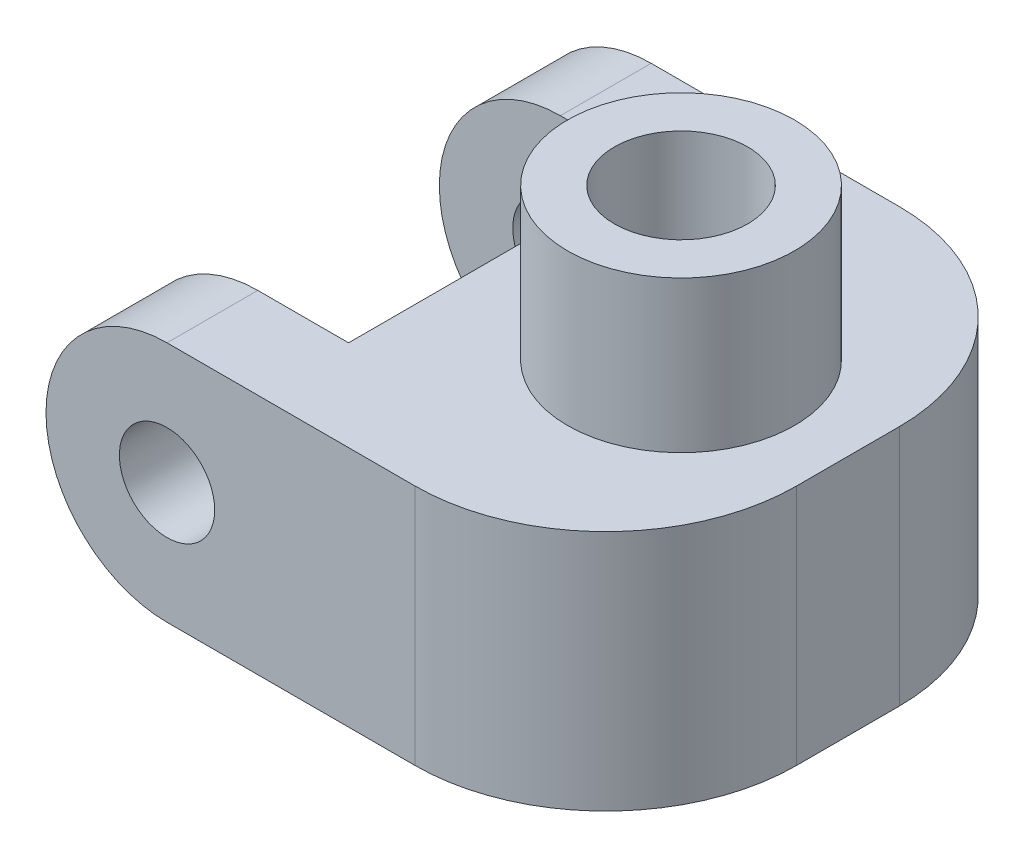
SolidWorks part; units mm, degrees
ref_plane "Front Plane" through (0, 0, 0) normal (0, 0, 1) x (1, 0, 0)
ref_plane "Top Plane" through (0, 0, 0) normal (0, 1, 0) x (1, 0, 0)
ref_plane "Right Plane" through (0, 0, 0) normal (1, 0, 0) x (0, 0, -1)
sketch "Sketch2" plane through (0, 0, 0) normal (0, 0, 1) x (1, 0, 0)
  line L0 (0, 5.08) -> (3.81, 5.08)
  line L1 (3.81, 5.08) -> (3.81, -5.08)
  line L2 (3.81, -5.08) -> (0, -5.08)
  line L3 (0, 0) -> (0, 5.08) construction
  line L4 (3.81, 5.08) -> (8.89, 5.08)
  line L5 (3.81, 5.08) -> (3.81, -5.08) construction
  line L6 (3.81, -5.08) -> (8.89, -5.08)
  line L7 (8.89, 5.08) -> (8.89, -5.08)
  line L12 (8.89, -5.08) -> (18.415, -5.08)
  line L13 (8.89, -5.08) -> (8.89, 5.08)
  line L14 (8.89, 5.08) -> (18.415, 5.08)
  line L15 (18.415, -5.08) -> (18.415, 5.08)
  circle A0 centre (0, 0) radius 2
  circle A1 centre (0, 0) radius 5.08
  point P13 (18.415, 3.1795)
  point P14 (0, 0)
  dimension "D1" = 4
  dimension "D2" = 10.16
  dimension "D3" = 3.81
  dimension "D4" = 5.08
  dimension "D5" = 9.525
extrude "Boss-Extrude1" add sketch "Sketch2" along normal blind 20.32
ref_plane "Plane1" through (0, 0, 10.16) normal (0, 0, 1) x (1, 0, 0)
sketch "Sketch3" plane through (0, 0, 10.16) normal (0, 0, 1) x (1, 0, 0)
  line L20 (3.81, -5.08) -> (0, -5.08) construction
  line L23 (3.81, 5.08) -> (3.81, -5.08) construction
  line L28 (3.81, 5.08) -> (8.89, 5.08) construction
  line L29 (8.89, 5.08) -> (8.89, -5.08) construction
  line L30 (3.81, -5.08) -> (8.89, -5.08) construction
  line L31 (0, 5.08) -> (3.81, 5.08) construction
  line L32 (3.81, -5.08) -> (0, -5.08)
  line L33 (3.81, 5.08) -> (3.81, -5.08)
  line L34 (3.81, 5.08) -> (8.89, 5.08)
  line L35 (8.89, 5.08) -> (8.89, -5.08)
  line L36 (3.81, -5.08) -> (8.89, -5.08)
  line L37 (0, 5.08) -> (3.81, 5.08)
  circle A1 centre (0, 0) radius 5.08
  circle A5 centre (0, 0) radius 5.08
  circle A7 centre (0, 0) radius 2
  circle A8 centre (0, 0) radius 2
  dimension "D1" = 0
  dimension "D2" = 0
extrude "Cut-Extrude1" cut sketch "Sketch3" against normal mid plane 12.7 contours L33 A5 A8 | A5 L33 L37 | A5 L32 L33
sketch "Sketch5" [suppressed] plane through (15.24, 0, 0) normal (1, 0, 0) x (0, 0, -1)
  circle A0 centre (-10.16, 0) radius 4.7625 construction
  circle A1 centre (-10.16, 0) radius 4.7625 construction
  circle A2 centre (-10.16, 0) radius 2.8
  dimension "D1" = 5.6
extrude "Cut-Extrude2" [suppressed] cut sketch "Sketch5" against normal blind 4.7
chamfer "Chamfer2" [suppressed] distance 2.54 angle 10
sketch "Sketch6" plane through (0, 5.08, 0) normal (0, 1, 0) x (1, 0, 0)
  line L0 (18.415, -20.32) -> (18.415, 0) construction
  circle A0 centre (11.415, -10.16) radius 4.7625
  point P2 (18.415, -10.16)
  point P3 (0, 0)
  dimension "D1" = 9.525
  dimension "D2" = 7
extrude "Boss-Extrude2" add sketch "Sketch6" along normal blind 6.35
sketch "Sketch7" plane through (0, 11.43, 0) normal (0, 1, 0) x (1, 0, 0)
  circle A0 centre (11.415, -10.16) radius 4.7625 construction
  circle A1 centre (11.415, -10.16) radius 4.7625
  circle A2 centre (11.415, -10.16) radius 2.8
  dimension "D1" = 5.6
extrude "Cut-Extrude3" cut sketch "Sketch7" against normal blind 5 contours A2
chamfer "Chamfer3" distance 7.62 angle 30 1 edges at (3.81, -5.08, 10.16)
fillet "Fillet1" radius 8 2 edges at (18.415, 0, 0) (18.415, 0, 20.32)
